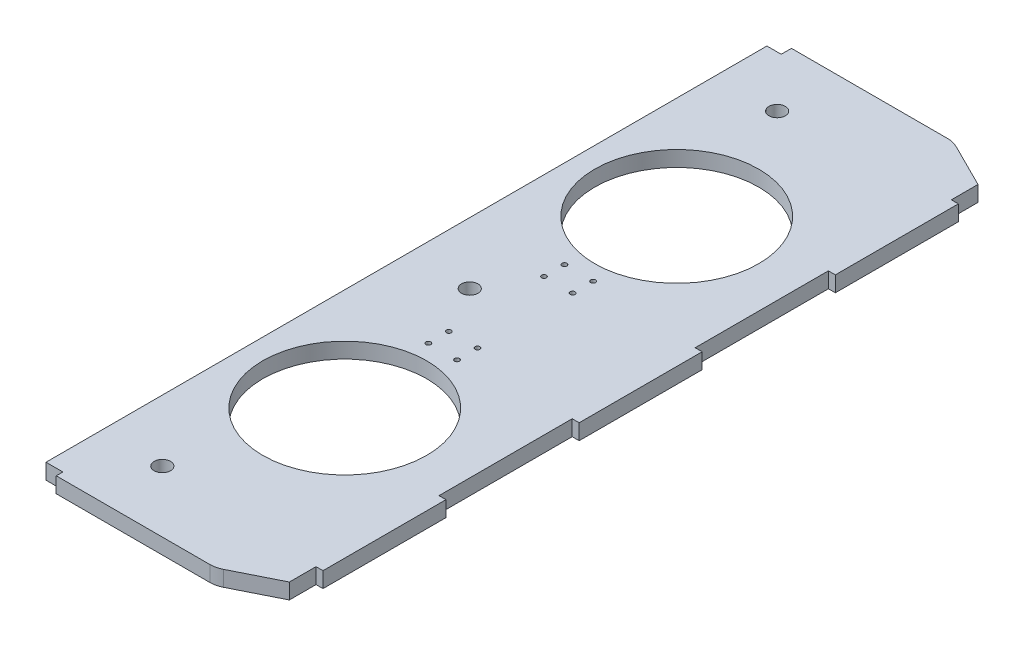
SolidWorks part; units mm, degrees
material "Acrylic (Medium-high impact)"
ref_plane "Front Plane" through (0, 0, 0) normal (0, 0, 1) x (1, 0, 0)
ref_plane "Top Plane" through (0, 0, 0) normal (0, 1, 0) x (1, 0, 0)
ref_plane "Right Plane" through (0, 0, 0) normal (1, 0, 0) x (0, 0, -1)
sketch "Sketch1" plane through (0, 0, 0) normal (0, 1, 0) x (1, 0, 0)
  line L0 (0, 0) -> (0, 457.2)
  line L1 (0, 457.2) -> (139.7, 457.2)
  line L10 (139.7, 457.2) -> (139.7, 0)
  line L11 (139.7, 0) -> (0, 0)
  line L12 (0, 228.6) -> (139.7, 228.6) construction
  circle A0 centre (63.5, 125.73) radius 50.8
  circle A1 centre (38.1, 38.1) radius 5.08
  circle A3 centre (38.1, 419.1) radius 5.08
  circle A4 centre (63.5, 331.47) radius 50.8
  circle A5 centre (38.1, 228.6) radius 5.08
  dimension "D11" = 10.16
  dimension "D17" = 10.16
  dimension "D3" = 101.6
  dimension "D4" = 10.16
  dimension "D7" = 82.55
  dimension "D2" = 63.5
  dimension "Length of Rib" = 457.2
  dimension "D5" = 38.1
  dimension "D6" = 190.5
  dimension "D12" = 38.1
  dimension "D13" = 38.1
  dimension "D18" = 38.1
  dimension "D19" = 38.1
  dimension "Width of Rib" = 139.7
extrude "Boss-Extrude1" add sketch "Sketch1" along normal blind 9.652
sketch "Sketch4" plane through (0, 9.652, 0) normal (0, 1, 0) x (1, 0, 0)
  line L0 (10.4524, 4.1148) -> (10.4524, -21.2852) construction
  line L1 (0, 0) -> (10.4524, 0)
  line L2 (0, 0) -> (0, 4.1148)
  line L3 (0, 4.1148) -> (10.4524, 4.1148)
  line L4 (10.4524, 0) -> (10.4524, 4.1148)
  line L6 (0, 457.2) -> (8.8649, 457.2)
  line L7 (0, 457.2) -> (0, 450.85)
  line L8 (0, 450.85) -> (8.8649, 450.85)
  line L9 (8.8649, 457.2) -> (8.8649, 450.85)
extrude "Cut-Extrude1" cut sketch "Sketch4" against normal through all
chamfer "Chamfer1" distance 15.24 distance2 30.48 1 edges at (139.7, 4.826, -457.2)
chamfer "Chamfer2" distance 30.48 distance2 15.24 1 edges at (139.7, 4.826, 0)
fillet "Fillet2" radius 15.24 2 edges at (109.22, 4.826, -457.2) (109.22, 4.826, 0)
sketch "Sketch5" plane through (139.7, 0, 0) normal (1, 0, 0) x (0, 0, -1)
  line L0 (15.24, 9.652) -> (441.96, 9.652) construction
  line L1 (31.75, 9.652) -> (107.95, 9.652)
  line L2 (31.75, 9.652) -> (31.75, 0)
  line L3 (31.75, 0) -> (107.95, 0)
  line L4 (107.95, 9.652) -> (107.95, 0)
  line L5 (15.24, 0) -> (441.96, 0) construction
  line L6 (0, 0) -> (0, 9.652) construction
  line L7 (190.5, 9.652) -> (190.5, 0)
  line L8 (190.5, 9.652) -> (266.7, 9.652)
  line L9 (190.5, 0) -> (266.7, 0)
  line L10 (266.7, 9.652) -> (266.7, 0)
  line L11 (349.25, 9.652) -> (349.25, 0)
  line L12 (349.25, 9.652) -> (425.45, 9.652)
  line L13 (349.25, 0) -> (425.45, 0)
  line L14 (425.45, 9.652) -> (425.45, 0)
  dimension "D1" = 31.75
  dimension "D2" = 76.2
  dimension "D3" = 3
extrude "Boss-Extrude2" add sketch "Sketch5" along normal blind 4.318
sketch "Sketch7" plane through (0, 9.652, 0) normal (0, 1, 0) x (1, 0, 0)
  line L0 (10.4524, 0) -> (105.6223, 0) construction
  line L1 (139.7, 107.95) -> (139.7, 190.5) construction
  line L2 (72.39, 186.436) -> (72.39, 199.136) construction
  line L4 (72.39, 186.436) -> (54.61, 186.436) construction
  line L5 (54.61, 186.436) -> (54.61, 199.136) construction
  line L6 (54.61, 199.136) -> (72.39, 199.136) construction
  point P0 (72.39, 186.436)
  point P2 (54.61, 186.436)
  point P4 (54.61, 199.136)
  point P6 (72.39, 199.136)
  dimension "D1" = 186.436
  dimension "D2" = 67.31
  dimension "D3" = 17.78
  dimension "D4" = 12.7
  dimension "D5" = 12.7
  dimension "D6" = 17.78
hole_wizard "Ø3.0 (3) Diameter Hole1" positions "Sketch7" profile "Sketch8" hole size "Ø3.0" standard "ANSI Metric" end condition up to next
sketch "Sketch8" plane through (72.39, 9.652, -186.436) normal (1, 0, 0) x (0, 0, 1)
  line L0 (0, 0) -> (0, 9.652)
  line L1 (0, 9.652) -> (1.5, 9.652)
  line L2 (1.5, 9.652) -> (1.5, 0)
  line L5 (1.5, 0) -> (0, 0)
  line L11 (0, -6.35) -> (0, 107.95) construction
  dimension "Thru Hole Dia." = 3
  dimension "Thru Hole Depth" = 9.652
sketch "Sketch9" plane through (0, 9.652, 0) normal (0, 1, 0) x (1, 0, 0)
  line L0 (144.018, 228.6) -> (-0.0043, 228.6) construction
  line L1 (144.018, 266.7) -> (144.018, 190.5) construction
ref_plane "Plane1" through (0, 0, -228.6) normal (0, 0, 1) x (1, 0, 0)
mirror "Mirror1" about plane through (0, 0, -228.6) normal (0, 0, 1) of "Ø3.0 (3) Diameter Hole1"
